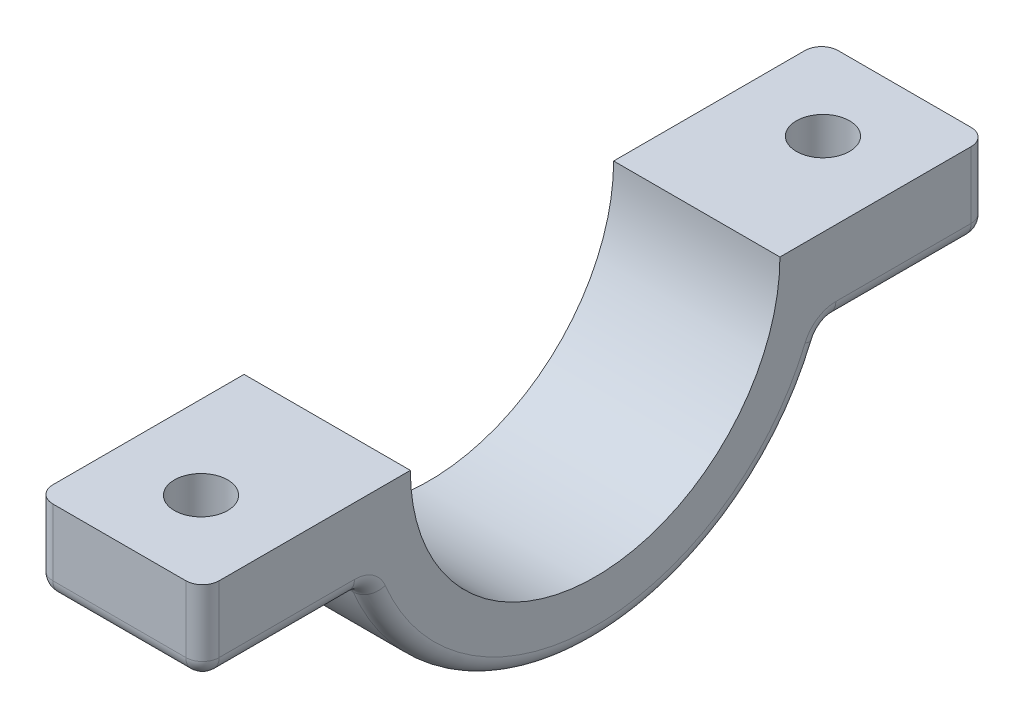
SolidWorks part; units mm, degrees
ref_plane "Front Plane" through (0, 0, 0) normal (0, 0, 1) x (1, 0, 0)
ref_plane "Top Plane" through (0, 0, 0) normal (0, 1, 0) x (1, 0, 0)
ref_plane "Right Plane" through (0, 0, 0) normal (1, 0, 0) x (0, 0, -1)
sketch "Sketch4" plane through (0, 0, 0) normal (1, 0, 0) x (0, 0, -1)
  line L0 (-23.6125, 0) -> (-11.1125, 0)
  line L2 (-23.6125, 0) -> (-23.6125, -5)
  line L3 (-23.6125, -5) -> (-13.7899, -5)
  line L4 (23.6125, 0) -> (23.6125, -5)
  line L5 (13.7899, -5) -> (23.6125, -5)
  line L6 (11.1125, 0) -> (23.6125, 0)
  arc A0 (-11.1125, 0) -> (11.1125, 0) centre (0, 0) ccw
  arc A2 (-13.7899, -5) -> (13.7899, -5) centre (0, 0) ccw
  dimension "D5" = 5
  dimension "D2" = 22.225
  dimension "D1" = 12.5
  dimension "D3" = 12.5
  dimension "D4" = 5
extrude "Clamp Extrude" add sketch "Sketch4" along normal blind 10
sketch "Hole" plane through (0, -5, 0) normal (0, -1, 0) x (1, 0, 0)
  line L2 (10, 23.6125) -> (0, 23.6125) construction
  line L3 (10, 13.7899) -> (0, 13.7899) construction
  line L4 (0, 23.6125) -> (0, 13.7899) construction
  line L5 (10, 23.6125) -> (10, 13.7899) construction
  line L6 (0, 0) -> (10, 0)
  line L7 (0, 13.7899) -> (0, -13.7899) construction
  line L8 (10, -13.7899) -> (10, 13.7899) construction
  circle A0 centre (5, 18.7012) radius 1.6
  circle A1 centre (5, -18.7012) radius 1.6
  dimension "D1" = 3.2
  dimension "D2" = 9.8226
  dimension "D3" = 4.9113
  dimension "D4" = 10
  dimension "D5" = 5
extrude "Holes Cut-Extrude" cut sketch "Hole" against normal through all contours A0 | A1
fillet "Fillet1" radius 1 14 edges at (10, -5, -18.7012) (0, -5, -18.7012) (10, -14.6684, 0) (0, -14.6684, 0) (0, -2.5, 23.6125) (10, -2.5, 23.6125) (10, -2.5, -23.6125) (0, -2.5, -23.6125) (5, -5, -23.6125) (5, -5, -13.7899) (5, -5, 13.7899) (10, -5, 18.7012) (5, -5, 23.6125) (0, -5, 18.7012)
equation "\"D3@Hole\"=\"D2@Hole\"/2"
equation "\"D5@Hole\"=\"D4@Hole\"/2"
equation "\"D3@Sketch4\"=\"D1@Sketch4\""
